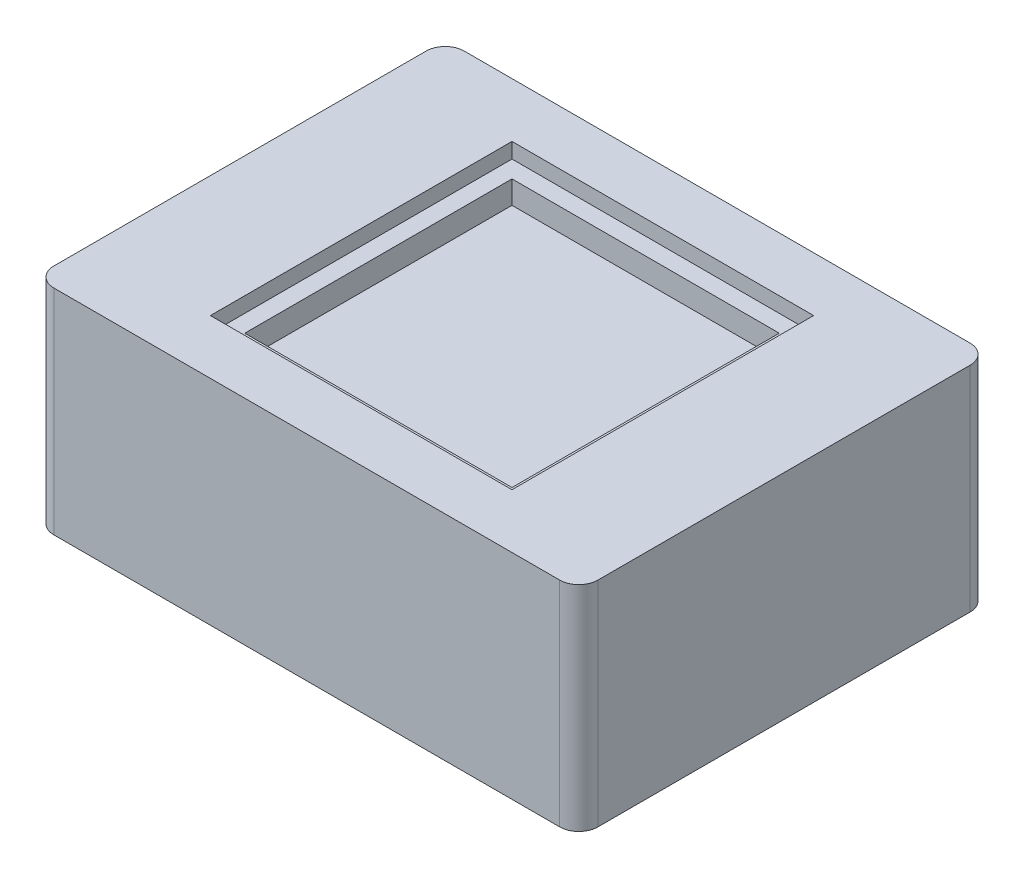
SolidWorks part; units mm, degrees
ref_plane "Front" through (0, 0, 0) normal (0, 0, 1) x (1, 0, 0)
ref_plane "Top" through (0, 0, 0) normal (0, 1, 0) x (1, 0, 0)
ref_plane "Right" through (0, 0, 0) normal (1, 0, 0) x (0, 0, -1)
sketch "草图1" plane through (0, 0, 0) normal (0, 1, 0) x (1, 0, 0)
  line L1 (-14.25, 10.75) -> (14.25, 10.75)
  line L2 (-14.25, 10.75) -> (-14.25, -10.75)
  line L3 (-14.25, -10.75) -> (14.25, -10.75)
  line L4 (14.25, 10.75) -> (14.25, -10.75)
  line L5 (-14.25, 10.75) -> (14.25, -10.75) construction
  line L6 (-14.25, -10.75) -> (14.25, 10.75) construction
  point P0 (0, 0)
  dimension "D1" = 21.5
  dimension "D2" = 28.5
extrude "凸台-拉伸1" add sketch "草图1" along normal blind 11.2
fillet "圆角1" radius 1 4 edges at (14.25, 5.6, 10.75) (-14.25, 5.6, 10.75) (-14.25, 5.6, -10.75) (14.25, 5.6, -10.75)
sketch "草图3" plane through (0, 11.2, 0) normal (0, 1, 0) x (1, 0, 0)
  line L1 (-7, 7) -> (7, 7)
  line L2 (-7, 7) -> (-7, -7)
  line L3 (-7, -7) -> (7, -7)
  line L4 (7, 7) -> (7, -7)
  line L5 (-7, 7) -> (7, -7) construction
  line L6 (-7, -7) -> (7, 7) construction
  point P0 (0, 0)
  dimension "D1" = 14
extrude "切除-拉伸2" cut sketch "草图3" against normal blind 2 contours L2 L1 L4 L3
sketch "草图4" plane through (0, 11.2, 0) normal (0, 1, 0) x (1, 0, 0)
  line L0 (-7, -7) -> (7, -7) construction
  line L1 (-7.9, 7.9) -> (7.9, 7.9)
  line L2 (-7.9, 7.9) -> (-7.9, -7.9)
  line L3 (-7.9, -7.9) -> (7.9, -7.9)
  line L4 (7.9, 7.9) -> (7.9, -7.9)
  line L5 (-7.9, 7.9) -> (7.9, -7.9) construction
  line L6 (-7.9, -7.9) -> (7.9, 7.9) construction
  point P0 (0, 0)
  dimension "D1" = 0.9
extrude "切除-拉伸3" cut sketch "草图4" against normal blind 0.8 contours L2 L1 L4 L3
